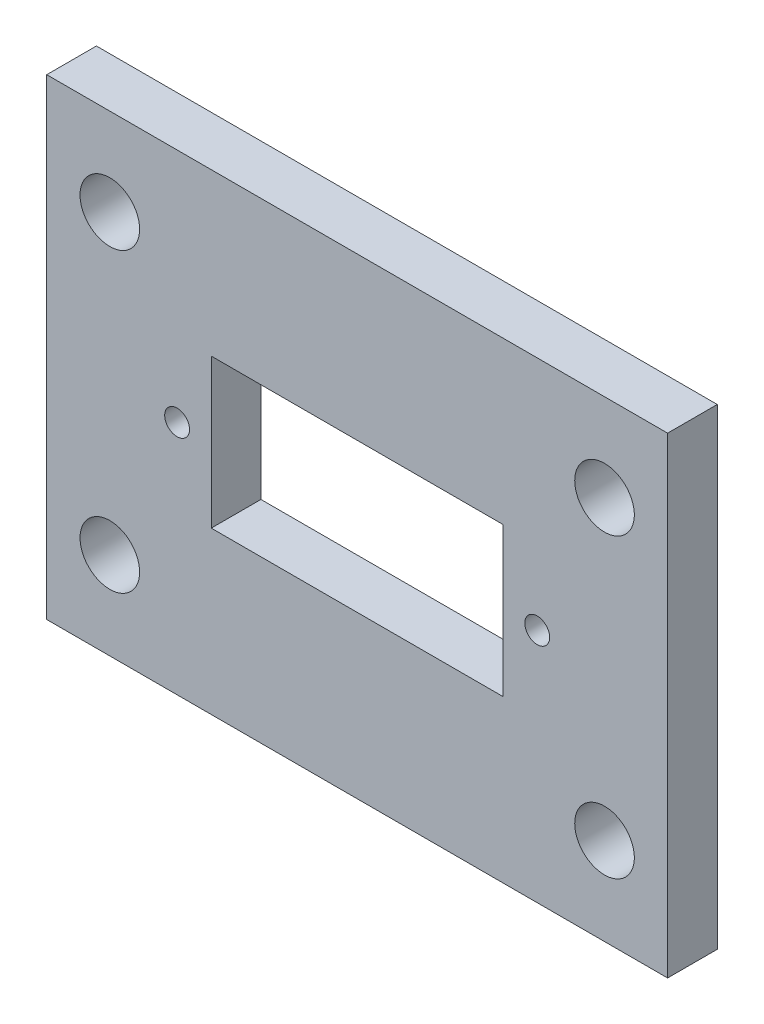
SolidWorks part; units mm, degrees
ref_plane "Front Plane" through (0, 0, 0) normal (0, 0, 1) x (1, 0, 0)
ref_plane "Top Plane" through (0, 0, 0) normal (0, 1, 0) x (1, 0, 0)
ref_plane "Right Plane" through (0, 0, 0) normal (1, 0, 0) x (0, 0, -1)
sketch "Sketch1" plane through (0, 0, 0) normal (0, 0, 1) x (1, 0, 0)
  line L0 (19.92, -7.045) -> (19.92, -30.955) construction
  line L1 (25, 0) -> (25, -38)
  line L2 (11.75, -13) -> (11.75, -25)
  line L5 (0, -13) -> (0, -25)
  line L6 (-11.75, -13) -> (11.75, -13)
  line L7 (-11.75, -13) -> (-11.75, -25)
  line L8 (-11.75, -25) -> (11.75, -25)
  line L10 (-25, 0) -> (25, 0)
  line L11 (-25, 0) -> (-25, -38)
  line L12 (-25, -38) -> (25, -38)
  line L14 (-19.92, -7.045) -> (-19.92, -30.955) construction
  line L16 (0, 0) -> (0, -38) construction
  circle A2 centre (-19.92, -7.045) radius 2.4
  circle A3 centre (-19.92, -30.955) radius 2.4
  circle A4 centre (19.92, -30.955) radius 2.4
  circle A5 centre (19.92, -7.045) radius 2.4
  point P0 (-18, -30.955)
  dimension "D12" = 4.8
  dimension "D2" = 25
  dimension "D3" = 23.91
  dimension "D4" = 12
  dimension "D6" = 7.045
  dimension "D7" = 13
  dimension "D8" = 38
  dimension "D9" = 11.75
  dimension "D13" = 19.92
extrude "Boss-Extrude1" add sketch "Sketch1" along normal blind 4 contours L10 L1 L12 L11 | A2 | A3 | L6 L2 L8 L7 | A5 | A4
sketch "Sketch2" plane through (0, 0, 4) normal (0, 0, 1) x (1, 0, 0)
  line L0 (-25, 0) -> (-25, -38) construction
  line L2 (-25, 0) -> (25, 0) construction
  circle A0 centre (-14.5, -19) radius 1
  circle A1 centre (14.5, -19) radius 1
  point P6 (0, 0)
  point P9 (0, 0)
  point P10 (0, 0)
  point P11 (0, 0)
  dimension "D1" = 2
  dimension "D2" = 29
  dimension "D3" = 10.5
  dimension "D4" = 19
extrude "Cut-Extrude1" cut sketch "Sketch2" against normal up to next
